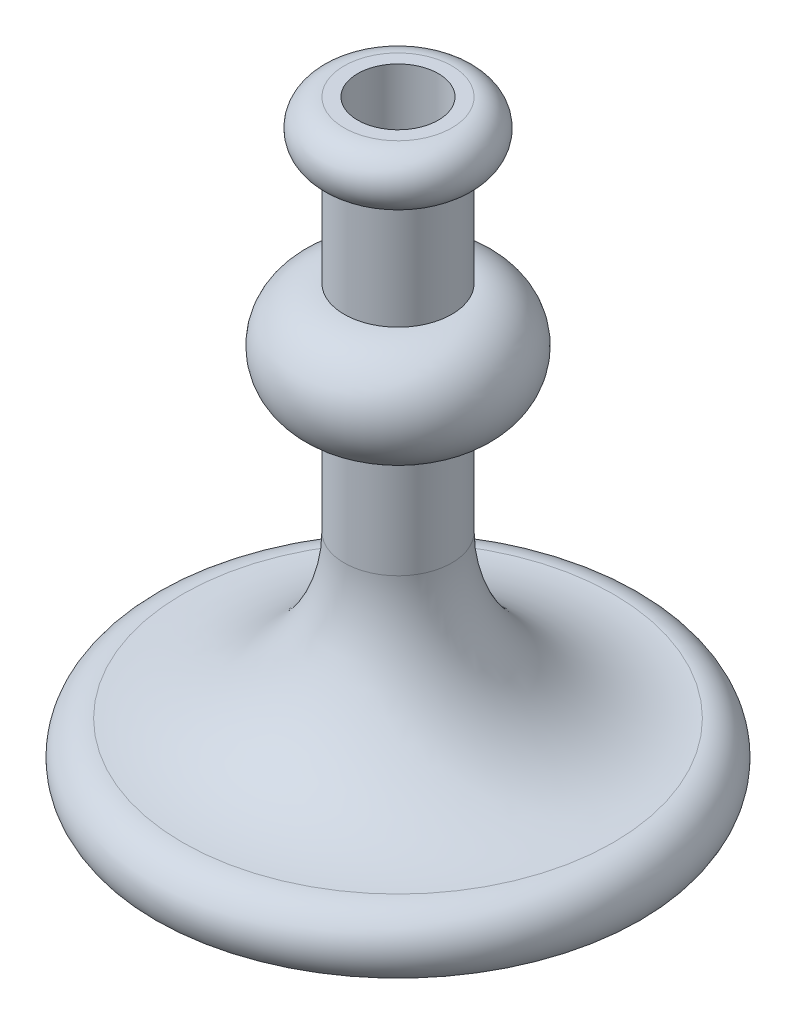
SolidWorks part; units mm, degrees
ref_plane "Front Plane" through (0, 0, 0) normal (0, 0, 1) x (1, 0, 0)
ref_plane "Top Plane" through (0, 0, 0) normal (0, 1, 0) x (1, 0, 0)
ref_plane "Right Plane" through (0, 0, 0) normal (1, 0, 0) x (0, 0, -1)
sketch "Sketch1" plane through (0, 0, 0) normal (0, 0, 1) x (1, 0, 0)
  line L0 (0, 0) -> (2286, 0)
  line L1 (0, 0) -> (0, 5588)
  line L2 (0, 5588) -> (508, 5588)
  line L3 (508, 5080) -> (508, 4064)
  line L4 (508, 3048) -> (508, 2032)
  arc A0 (508, 5588) -> (508, 5080) centre (508, 5334) cw
  arc A1 (508, 4064) -> (508, 3048) centre (508, 3556) cw
  arc A2 (508, 2032) -> (2032, 508) centre (2032, 2032) ccw
  arc A3 (2032, 508) -> (2286, 0) centre (2032, 190.5) cw
  point P14 (508, 4064)
  point P15 (508, 5080)
  point P16 (508, 5080)
  point P17 (508, 3556)
  point P18 (508, 3048)
  point P19 (2032, 508)
  point P20 (508, 3048)
  point P21 (0, 0)
  point P22 (0, 0)
  point P23 (508, 3556)
  point P24 (0, 0)
  dimension "D4" = 254
  dimension "D5" = 2032
  dimension "D6" = 508
  dimension "D8" = 1524
  dimension "D9" = 317.5
  dimension "D1" = 2286
  dimension "D2" = 5588
  dimension "D3" = 508
  dimension "D7" = 1016
revolve "Revolve1" add sketch "Sketch1" angle 360 about L1
sketch "Sketch2" plane through (0, 5588, 0) normal (0, 1, 0) x (1, 0, 0)
  circle A2 centre (0, 0) radius 381
  circle A3 centre (0, 0) radius 381
  dimension "D1" = 127
extrude "Cut-Extrude1" cut sketch "Sketch2" against normal through all
